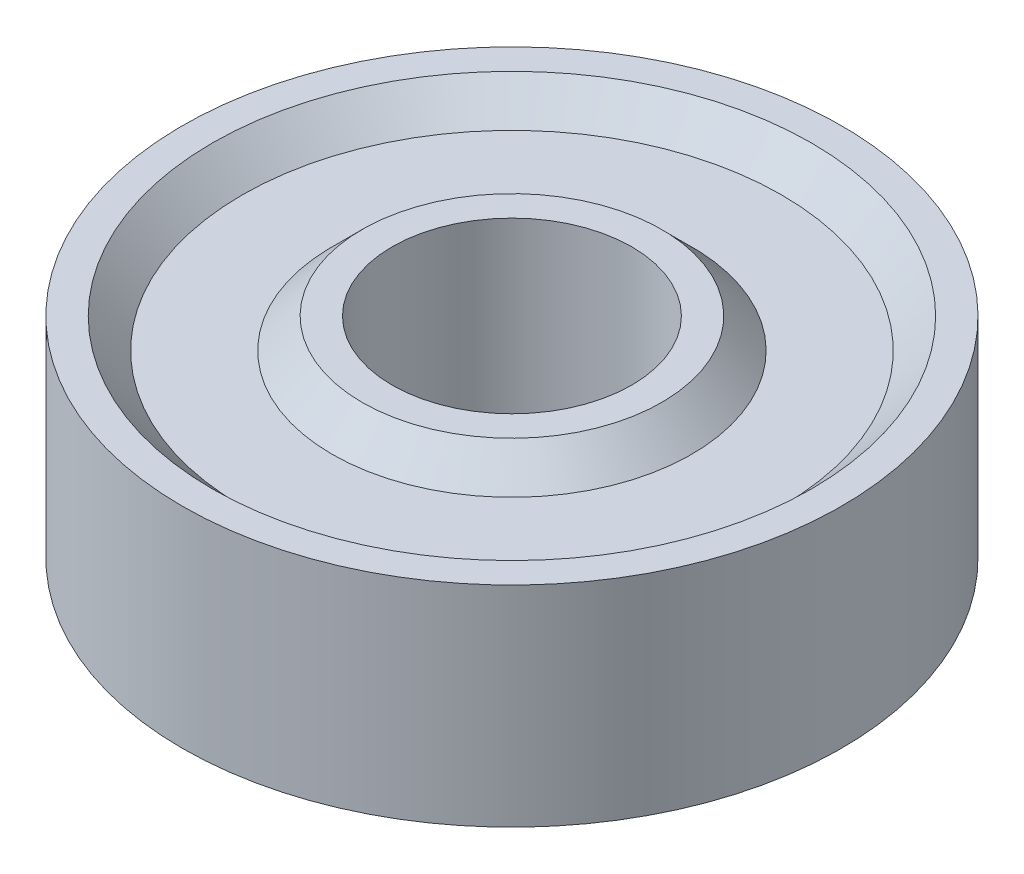
SolidWorks part; units mm, degrees
ref_plane "Front Plane" through (0, 0, 0) normal (0, 0, 1) x (1, 0, 0)
ref_plane "Top Plane" through (0, 0, 0) normal (0, 1, 0) x (1, 0, 0)
ref_plane "Right Plane" through (0, 0, 0) normal (1, 0, 0) x (0, 0, -1)
sketch "Sketch1" plane through (0, 0, 0) normal (0, 0, 1) x (1, 0, 0)
  line L0 (4, 3.5) -> (4, -3.5)
  line L6 (11, -3.5) -> (11, 3.5)
  line L7 (11, 3.5) -> (10, 3.5)
  line L8 (10, 3.5) -> (9, 2.5)
  line L9 (9, 2.5) -> (6, 2.5)
  line L10 (6, 2.5) -> (5, 3.5)
  line L11 (5, 3.5) -> (4, 3.5)
  line L12 (0, 0) -> (0, -6.6547) construction
  line L13 (0, 0) -> (-6.9726, 0) construction
  line L14 (5, -3.5) -> (4, -3.5)
  line L15 (6, -2.5) -> (5, -3.5)
  line L16 (9, -2.5) -> (6, -2.5)
  line L17 (10, -3.5) -> (9, -2.5)
  line L18 (11, -3.5) -> (10, -3.5)
  point P8 (4, 0)
  point P18 (11, 0)
  dimension "D1" = 4
  dimension "D2" = 11
  dimension "D3" = 3
  dimension "D4" = 1
  dimension "D5" = 1
  dimension "D7" = 3.5
revolve "Revolve1" add sketch "Sketch1" angle 360 about L12
